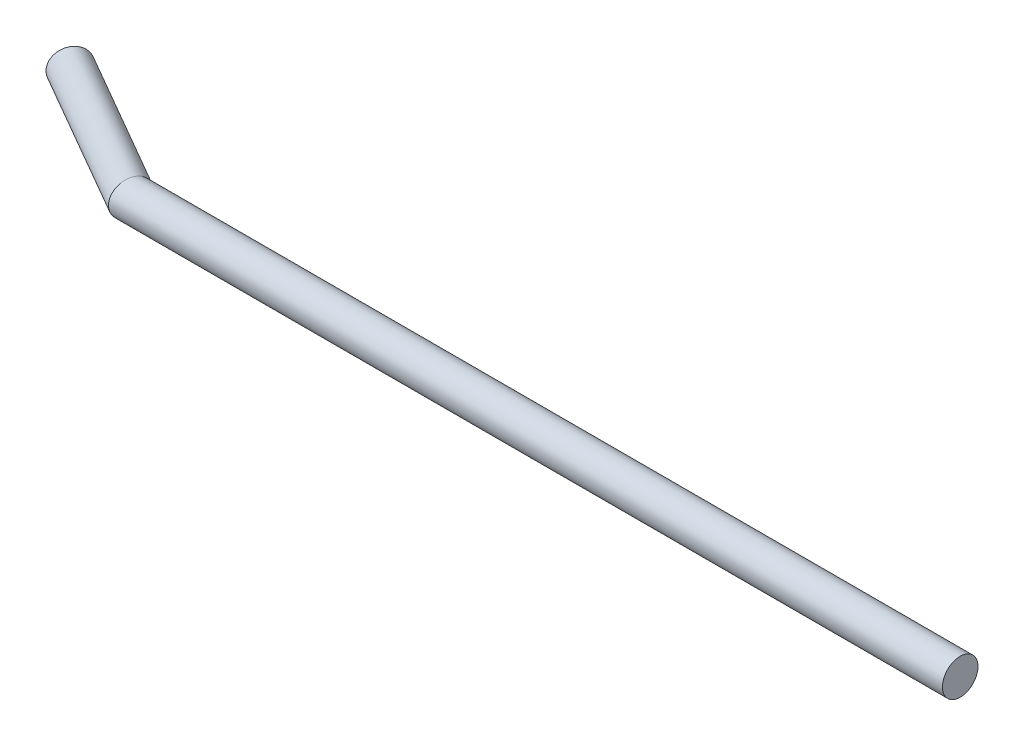
SolidWorks part; units mm, degrees
ref_plane "Front Plane" through (0, 0, 0) normal (0, 0, 1) x (1, 0, 0)
ref_plane "Top Plane" through (0, 0, 0) normal (0, 1, 0) x (1, 0, 0)
ref_plane "Right Plane" through (0, 0, 0) normal (1, 0, 0) x (0, 0, -1)
sketch "Sketch1" plane through (0, 0, 0) normal (0, 1, 0) x (1, 0, 0)
  line L0 (0, 0) -> (-70, 0)
  line L1 (-70, 0) -> (-82.1244, 7)
  dimension "D1" = 30
  dimension "D2" = 14
  dimension "D3" = 70
sketch "Sketch2" plane through (0, 0, 0) normal (1, 0, 0) x (0, 0, -1)
  circle A0 centre (0, 0) radius 1.5
  dimension "D1" = 3
sweep "Sweep1" add profiles "Sketch2" path "Sketch1"
